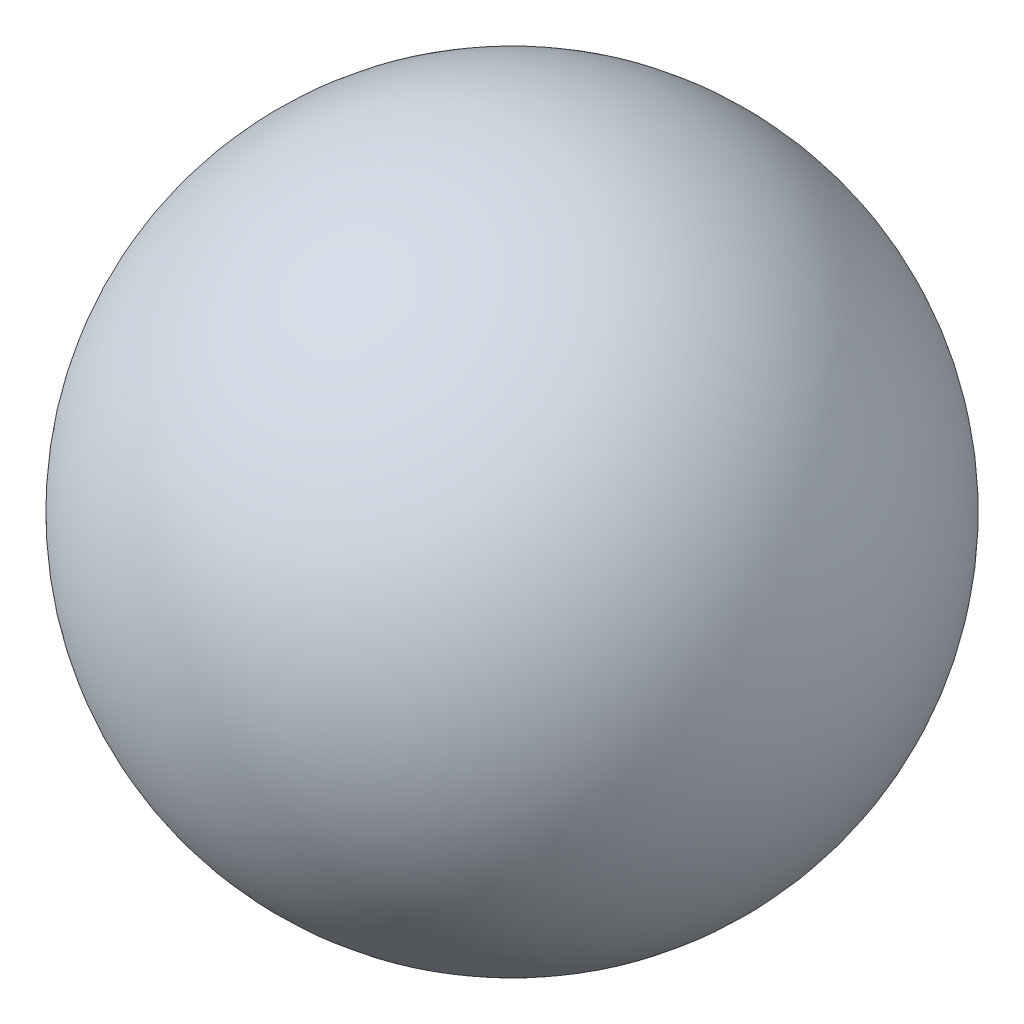
SolidWorks part; units mm, degrees
ref_plane "前视基准面" through (0, 0, 0) normal (0, 0, 1) x (1, 0, 0)
ref_plane "上视基准面" through (0, 0, 0) normal (0, 1, 0) x (1, 0, 0)
ref_plane "右视基准面" through (0, 0, 0) normal (1, 0, 0) x (0, 0, -1)
sketch "草图1" plane through (0, 0, 0) normal (0, 0, 1) x (1, 0, 0)
  line L0 (0, 1) -> (0, -1) construction
  line L1 (0, -1) -> (0, 1)
  arc A0 (0, -1) -> (0, 1) centre (0, 0) ccw
  dimension "D1" = 2
revolve "旋转1" add sketch "草图1" angle 360 about L0
sketch "草图2" plane through (0, 0, 0) normal (0, 1, 0) x (1, 0, 0)
  line L0 (0, 0) -> (0, 1.8142) construction
  line L1 (0, -1.1) -> (0, 1.1) construction
  line L2 (0, 0) -> (-1.3325, 0) construction
  line L3 (-1.1, 0) -> (1.1, 0) construction
sketch "草图3" plane through (0, 0, 0) normal (0, 0, 1) x (1, 0, 0)
  line L0 (0, 0) -> (0, 1.3341) construction
  line L1 (0, -1.1) -> (0, 1.1) construction
